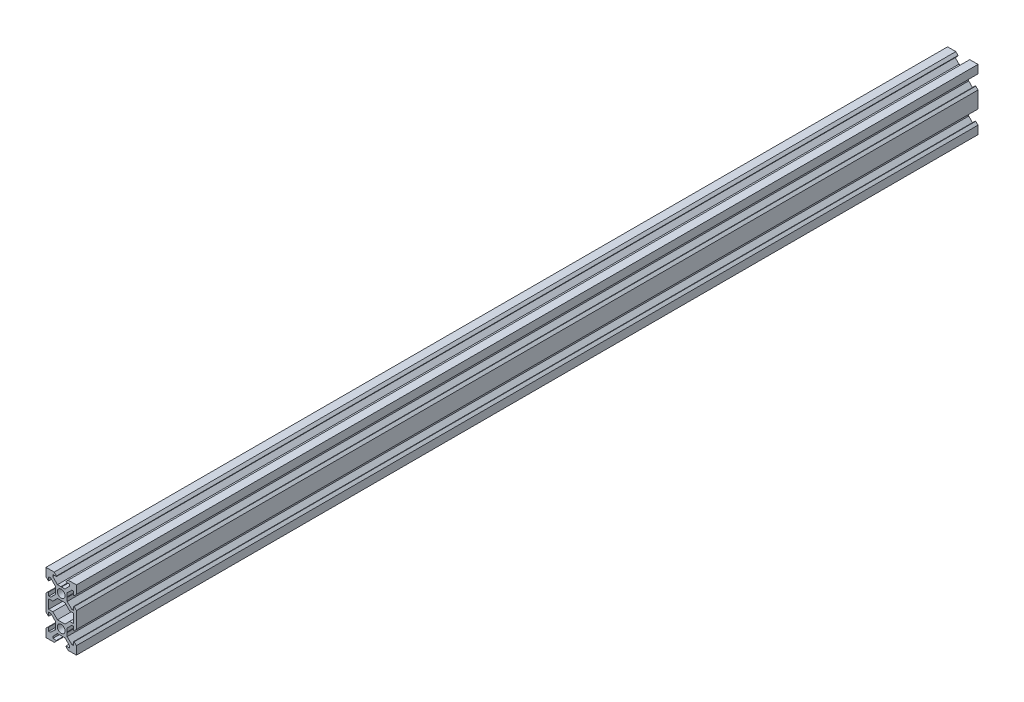
SolidWorks part; units mm, degrees
ref_plane "Спереди" through (0, 0, 0) normal (0, 0, 1) x (1, 0, 0)
ref_plane "Сверху" through (0, 0, 0) normal (0, 1, 0) x (1, 0, 0)
ref_plane "Справа" through (0, 0, 0) normal (1, 0, 0) x (0, 0, -1)
ref_plane "Плоскость4" through (0, 0, 792.9) normal (0, 0, 1) x (1, 0, 0)
sketch "Эскиз1" plane through (0, 0, 792.9) normal (0, 0, 1) x (1, 0, 0)
  line L0 (-2.4781, -3.9) -> (2.4781, -3.9)
  line L1 (2.4781, -3.9) -> (5.5, -7.002)
  line L2 (5.5, -7.002) -> (8.2, -7.002)
  line L3 (8.2, -7.002) -> (8.2, -12.998)
  line L4 (8.2, -12.998) -> (5.5, -12.998)
  line L5 (5.5, -12.998) -> (2.4781, -16.1)
  line L6 (2.4781, -16.1) -> (-2.4781, -16.1)
  line L7 (-2.4781, -16.1) -> (-5.5, -12.998)
  line L8 (-5.5, -12.998) -> (-8.2, -12.998)
  line L9 (-8.2, -12.998) -> (-8.2, -7.002)
  line L10 (-8.2, -7.002) -> (-5.5, -7.002)
  line L11 (-5.5, -7.002) -> (-2.4781, -3.9)
  line L12 (-8.2, -3.125) -> (-8.5064, -3.125)
  line L13 (-8.5064, -3.125) -> (-10, -4.58)
  line L14 (-10, -4.58) -> (-10, -15.42)
  line L15 (-10, -15.42) -> (-8.5064, -16.875)
  line L16 (-8.5064, -16.875) -> (-8.2, -16.875)
  line L17 (-8.2, -16.875) -> (-8.2, -14.5)
  line L18 (-8.2, -14.5) -> (-7.002, -14.5)
  line L19 (-7.002, -14.5) -> (-3.9, -17.5219)
  line L20 (-3.9, -17.5219) -> (-3.9, -19.8)
  line L21 (-3.9, -19.8) -> (-3.7, -20)
  line L22 (-3.7, -20) -> (-3.9, -20.2)
  line L23 (-3.9, -20.2) -> (-3.9, -22.4781)
  line L24 (-3.9, -22.4781) -> (-7.002, -25.5)
  line L25 (-7.002, -25.5) -> (-8.2, -25.5)
  line L26 (-8.2, -25.5) -> (-8.2, -23.125)
  line L27 (-8.2, -23.125) -> (-8.5064, -23.125)
  line L28 (-8.5064, -23.125) -> (-10, -24.58)
  line L29 (-10, -24.58) -> (-10, -30)
  line L30 (-10, -30) -> (-4.58, -30)
  line L31 (-4.58, -30) -> (-3.125, -28.5064)
  line L32 (-3.125, -28.5064) -> (-3.125, -28.2)
  line L33 (-3.125, -28.2) -> (-5.5, -28.2)
  line L34 (-5.5, -28.2) -> (-5.5, -27.002)
  line L35 (-5.5, -27.002) -> (-2.4781, -23.9)
  line L36 (-2.4781, -23.9) -> (-0.2, -23.9)
  line L37 (-0.2, -23.9) -> (0, -23.7)
  line L38 (0, -23.7) -> (0.2, -23.9)
  line L39 (0.2, -23.9) -> (2.4781, -23.9)
  line L40 (2.4781, -23.9) -> (5.5, -27.002)
  line L41 (5.5, -27.002) -> (5.5, -28.2)
  line L42 (5.5, -28.2) -> (3.125, -28.2)
  line L43 (3.125, -28.2) -> (3.125, -28.5064)
  line L44 (3.125, -28.5064) -> (4.58, -30)
  line L45 (4.58, -30) -> (10, -30)
  line L46 (10, -30) -> (10, -24.58)
  line L47 (10, -24.58) -> (8.5064, -23.125)
  line L48 (8.5064, -23.125) -> (8.2, -23.125)
  line L49 (8.2, -23.125) -> (8.2, -25.5)
  line L50 (8.2, -25.5) -> (7.002, -25.5)
  line L51 (7.002, -25.5) -> (3.9, -22.4781)
  line L52 (3.9, -22.4781) -> (3.9, -20.2)
  line L53 (3.9, -20.2) -> (3.7, -20)
  line L54 (3.7, -20) -> (3.9, -19.8)
  line L55 (3.9, -19.8) -> (3.9, -17.5219)
  line L56 (3.9, -17.5219) -> (7.002, -14.5)
  line L57 (7.002, -14.5) -> (8.2, -14.5)
  line L58 (8.2, -14.5) -> (8.2, -16.875)
  line L59 (8.2, -16.875) -> (8.5064, -16.875)
  line L60 (8.5064, -16.875) -> (10, -15.42)
  line L61 (10, -15.42) -> (10, -4.58)
  line L62 (10, -4.58) -> (8.5064, -3.125)
  line L63 (8.5064, -3.125) -> (8.2, -3.125)
  line L64 (8.2, -3.125) -> (8.2, -5.5)
  line L65 (8.2, -5.5) -> (7.002, -5.5)
  line L66 (7.002, -5.5) -> (3.9, -2.4781)
  line L67 (3.9, -2.4781) -> (3.9, -0.2)
  line L68 (3.9, -0.2) -> (3.7, 0)
  line L69 (3.7, 0) -> (3.9, 0.2)
  line L70 (3.9, 0.2) -> (3.9, 2.4781)
  line L71 (3.9, 2.4781) -> (7.002, 5.5)
  line L72 (7.002, 5.5) -> (8.2, 5.5)
  line L73 (8.2, 5.5) -> (8.2, 3.125)
  line L74 (8.2, 3.125) -> (8.5064, 3.125)
  line L75 (8.5064, 3.125) -> (10, 4.58)
  line L76 (10, 4.58) -> (10, 10)
  line L77 (10, 10) -> (4.58, 10)
  line L78 (4.58, 10) -> (3.125, 8.5064)
  line L79 (3.125, 8.5064) -> (3.125, 8.2)
  line L80 (3.125, 8.2) -> (5.5, 8.2)
  line L81 (5.5, 8.2) -> (5.5, 7.002)
  line L82 (5.5, 7.002) -> (2.4781, 3.9)
  line L83 (2.4781, 3.9) -> (0.2, 3.9)
  line L84 (0.2, 3.9) -> (0, 3.7)
  line L85 (0, 3.7) -> (-0.2, 3.9)
  line L86 (-0.2, 3.9) -> (-2.4781, 3.9)
  line L87 (-2.4781, 3.9) -> (-5.5, 7.002)
  line L88 (-5.5, 7.002) -> (-5.5, 8.2)
  line L89 (-5.5, 8.2) -> (-3.125, 8.2)
  line L90 (-3.125, 8.2) -> (-3.125, 8.5064)
  line L91 (-3.125, 8.5064) -> (-4.58, 10)
  line L92 (-4.58, 10) -> (-10, 10)
  line L93 (-10, 10) -> (-10, 4.58)
  line L94 (-10, 4.58) -> (-8.5064, 3.125)
  line L95 (-8.5064, 3.125) -> (-8.2, 3.125)
  line L96 (-8.2, 3.125) -> (-8.2, 5.5)
  line L97 (-8.2, 5.5) -> (-7.002, 5.5)
  line L98 (-7.002, 5.5) -> (-3.9, 2.4781)
  line L99 (-3.9, 2.4781) -> (-3.9, 0.2)
  line L100 (-3.9, 0.2) -> (-3.7, 0)
  line L101 (-3.7, 0) -> (-3.9, -0.2)
  line L102 (-3.9, -0.2) -> (-3.9, -2.4781)
  line L103 (-3.9, -2.4781) -> (-7.002, -5.5)
  line L104 (-7.002, -5.5) -> (-8.2, -5.5)
  line L105 (-8.2, -5.5) -> (-8.2, -3.125)
  circle A0 centre (0, 0) radius 2.55
  circle A1 centre (0, -20) radius 2.55
extrude "Бобышка-Вытянуть1" add sketch "Эскиз1" against normal blind 592.5
